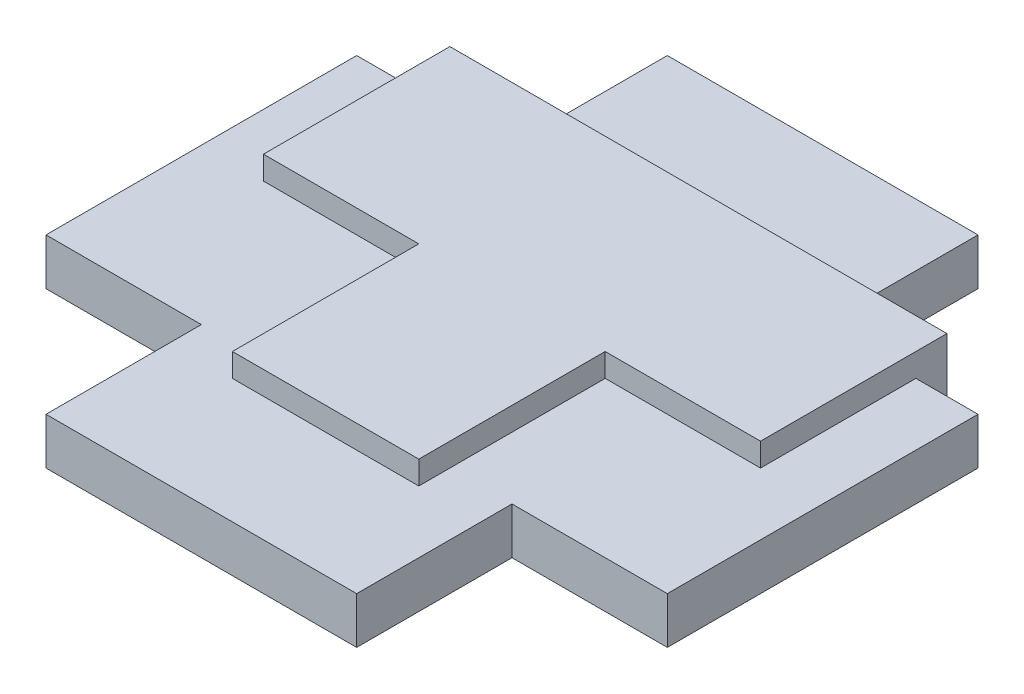
SolidWorks part; units mm, degrees
ref_plane "Front Plane" through (0, 0, 0) normal (0, 0, 1) x (1, 0, 0)
ref_plane "Top Plane" through (0, 0, 0) normal (0, 1, 0) x (1, 0, 0)
ref_plane "Right Plane" through (0, 0, 0) normal (1, 0, 0) x (0, 0, -1)
sketch "Sketch1" plane through (0, 0, 0) normal (0, 1, 0) x (1, 0, 0)
  line L1 (10, -10) -> (-10, -10)
  line L2 (10, -10) -> (10, 10)
  line L3 (10, 10) -> (-10, 10)
  line L4 (-10, -10) -> (-10, 10)
  line L5 (8, -8) -> (-8, -8) construction
  line L6 (8, -8) -> (8, 8) construction
  line L7 (8, 8) -> (-8, 8) construction
  line L8 (-8, -8) -> (-8, 8) construction
  line L9 (0, 8) -> (0, -8) construction
  line L10 (8, 0) -> (-8, 0) construction
  line L11 (-8, 0) -> (8, 0)
  line L12 (-8, 0) -> (-8, 6)
  line L13 (-8, 6) -> (8, 6)
  line L14 (8, 0) -> (8, 6)
  line L15 (3, 0) -> (-3, 0)
  line L16 (3, 0) -> (3, -6)
  line L17 (3, -6) -> (-3, -6)
  line L18 (-3, 0) -> (-3, -6)
  point P0 (0, 0)
  point P4 (0, 0)
  dimension "D1" = 20
  dimension "D2" = 20
  dimension "D3" = 16
  dimension "D4" = 16
  dimension "D5" = 6
  dimension "D6" = 6
  dimension "D7" = 6
  dimension "D8" = 3
extrude "Boss-Extrude2" add sketch "Sketch1" along normal blind 3 contours L11 L18 L17 L16 | L11 L14 L13 L12
ref_plane "Plane1" through (0, 1.5, 0) normal (0, 1, 0) x (1, 0, 0)
sketch "Sketch4" plane through (0, 1.5, 0) normal (0, 1, 0) x (1, 0, 0)
  line L1 (10, -10) -> (-10, -10) construction
  line L2 (10, -10) -> (10, 10) construction
  line L3 (10, 10) -> (-10, 10) construction
  line L4 (-10, -10) -> (-10, 10) construction
  line L5 (0, 10) -> (0, -10) construction
  line L6 (10, 0) -> (-10, 0) construction
  line L7 (5, -10) -> (-5, -10)
  line L8 (5, -10) -> (5, 10)
  line L9 (5, 10) -> (-5, 10)
  line L10 (-5, -10) -> (-5, 10)
  line L11 (0, 10) -> (0, -10) construction
  line L12 (5, 0) -> (-5, 0) construction
  line L13 (10, 5) -> (-10, 5)
  line L14 (10, 5) -> (10, -5)
  line L15 (10, -5) -> (-10, -5)
  line L16 (-10, 5) -> (-10, -5)
  line L17 (0, -5) -> (0, 5) construction
  line L18 (10, 0) -> (-10, 0) construction
  point P0 (0, 0)
  point P4 (0, 0)
  point P8 (0, 0)
  dimension "D1" = 20
  dimension "D2" = 20
  dimension "D3" = 10
  dimension "D4" = 10
extrude "Boss-Extrude3" add sketch "Sketch4" along normal blind 0.75 and the other way blind 0.75 contours L13 L16 L15 L10 | L15 L8 L13 L10 | L13 L8 L9 L10 | L15 L14 L13 L8 | L8 L15 L10 L7
